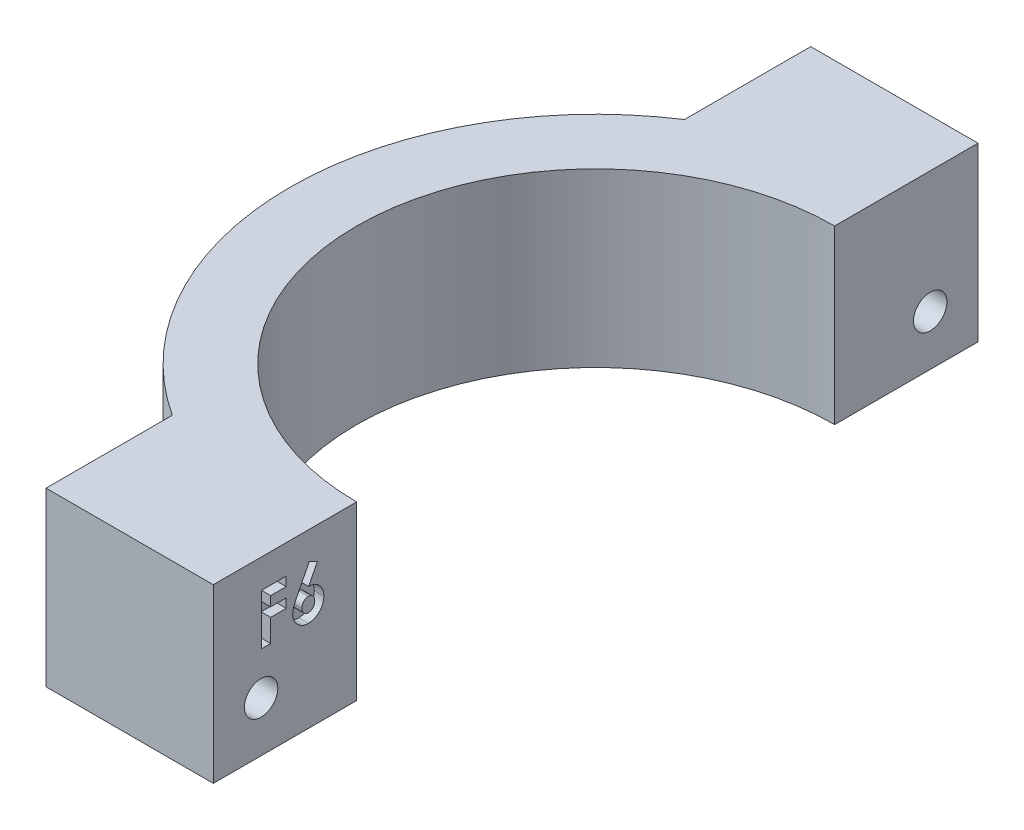
SolidWorks part; units mm, degrees
ref_plane "Front Plane" through (0, 0, 0) normal (0, 0, 1) x (1, 0, 0)
ref_plane "Top Plane" through (0, 0, 0) normal (0, 1, 0) x (1, 0, 0)
ref_plane "Right Plane" through (0, 0, 0) normal (1, 0, 0) x (0, 0, -1)
sketch "Sketch1" plane through (0, 0, 0) normal (0, 1, 0) x (1, 0, 0)
  line L0 (-46.9983, 32.5286) -> (-46.9983, -47.4714)
  line L1 (-46.9983, -47.4714) -> (-11.9983, -47.4714)
  line L2 (-11.9983, -47.4714) -> (-11.9983, -32.4714)
  line L3 (-46.9983, 32.5286) -> (-11.9983, 32.5286)
  line L4 (-11.9983, 32.5286) -> (-11.9983, 17.5286)
  line L5 (-29.4983, 32.5286) -> (-29.4983, 19.3194)
  line L6 (-29.4983, -34.2623) -> (-29.4983, -47.4714)
  arc A0 (-11.9983, 17.5286) -> (-11.9983, -32.4714) centre (-11.9983, -7.4714) ccw
  arc A1 (-11.9983, 24.5286) -> (-11.9983, -39.4714) centre (-11.9983, -7.4714) ccw
  dimension "D1" = 80
  dimension "D2" = 35
  dimension "D3" = 35
  dimension "D4" = 50
  dimension "D5" = 15
  dimension "D6" = 15
  dimension "D7" = 7
extrude "Boss-Extrude1" add sketch "Sketch1" along normal blind 18 contours A1 L4 L3 L5 | L4 A1 L2 A0 | A1 L6 L1 L2
sketch "Sketch2" plane through (-11.9983, 0, 0) normal (1, 0, 0) x (0, 0, -1)
  line L0 (-47.4714, 18) -> (-32.4714, 18) construction
  line L3 (32.5286, 18) -> (17.5286, 18) construction
  line L8 (32.5286, 18) -> (32.5286, 0) construction
  line L9 (-47.4714, 18) -> (-47.4714, 0) construction
  circle A0 centre (-42.4714, 5.25) radius 1.75
  circle A1 centre (27.5286, 5.25) radius 1.75
  dimension "D3" = 5
  dimension "D5" = 3.5
  dimension "D6" = 3.5
  dimension "D1" = 12.75
  dimension "D2" = 12.75
  dimension "D4" = 5
extrude "Cut-Extrude1" cut sketch "Sketch2" against normal through all
sketch "Sketch3" plane through (-11.9983, 0, 0) normal (1, 0, 0) x (0, 0, -1)
  text T0 "<b>F6</b>" font "Century Gothic" height in points 20
extrude "Cut-Extrude2" cut sketch "Sketch3" against normal blind 1
sketch "Sketch4" plane through (-29.4983, 0, 0) normal (-1, 0, 0) x (0, 0, 1)
  line L1 (-25.2832, 3.0046) -> (-24.4613, 6.0719)
  line L2 (-24.4613, 6.0719) -> (-26.7067, 8.3172)
  line L3 (-26.7067, 8.3172) -> (-29.7739, 7.4954)
  line L4 (-29.7739, 7.4954) -> (-30.5958, 4.4281)
  line L5 (-30.5958, 4.4281) -> (-28.3504, 2.1828)
  line L6 (-28.3504, 2.1828) -> (-25.2832, 3.0046)
  line L7 (44.3497, 2.6896) -> (45.6279, 5.5964)
  line L8 (45.6279, 5.5964) -> (43.7497, 8.1568)
  line L9 (43.7497, 8.1568) -> (40.5932, 7.8104)
  line L10 (40.5932, 7.8104) -> (39.315, 4.9036)
  line L11 (39.315, 4.9036) -> (41.1932, 2.3432)
  line L12 (41.1932, 2.3432) -> (44.3497, 2.6896)
  circle A0 centre (-27.5286, 5.25) radius 2.75 construction
  circle A1 centre (42.4714, 5.25) radius 2.75 construction
extrude "Cut-Extrude3" cut sketch "Sketch4" against normal blind 5
